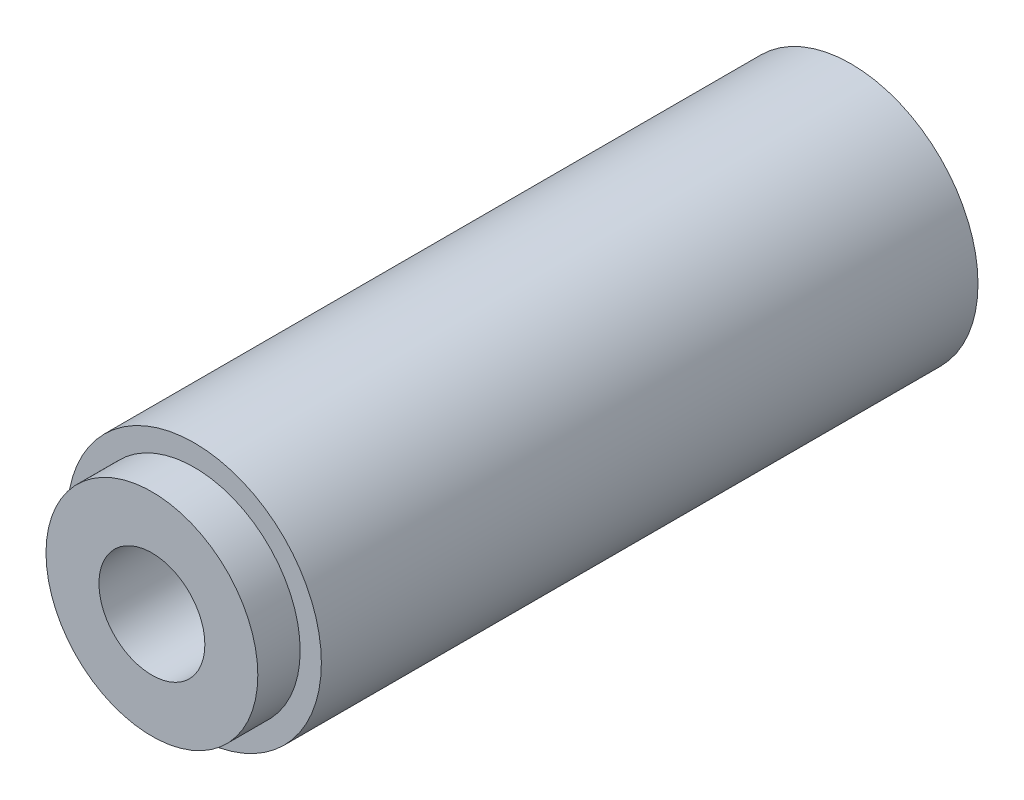
SolidWorks part; units mm, degrees
ref_plane "Front Plane" through (0, 0, 0) normal (0, 0, 1) x (1, 0, 0)
ref_plane "Top Plane" through (0, 0, 0) normal (0, 1, 0) x (1, 0, 0)
ref_plane "Right Plane" through (0, 0, 0) normal (1, 0, 0) x (0, 0, -1)
sketch "Sketch1" plane through (0, 0, 0) normal (0, 0, 1) x (1, 0, 0)
  circle A0 centre (0, 0) radius 6
extrude "Boss-Extrude1" add sketch "Sketch1" along normal blind 31
sketch "Sketch2" plane through (0, 0, 31) normal (0, 0, 1) x (1, 0, 0)
  circle A0 centre (0, 0) radius 5
extrude "Boss-Extrude2" add sketch "Sketch2" along normal blind 2
sketch "Sketch3" plane through (0, 0, 33) normal (0, 0, 1) x (1, 0, 0)
  circle A0 centre (0, 0) radius 2.5
extrude "Cut-Extrude1" cut sketch "Sketch3" against normal blind 5
